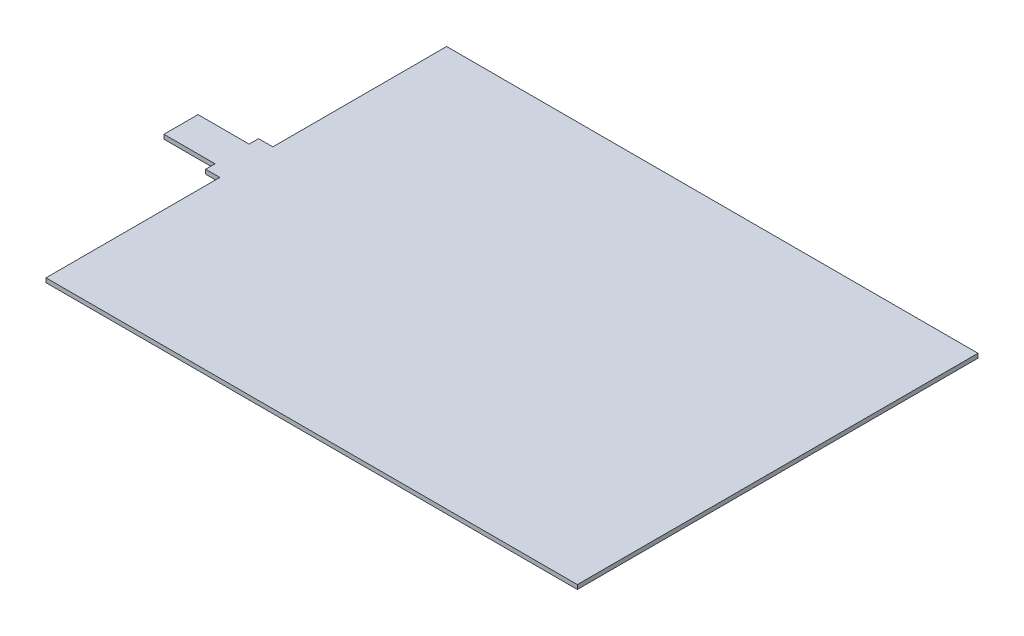
SolidWorks part; units mm, degrees
ref_plane "Front Plane" through (0, 0, 0) normal (0, 0, 1) x (1, 0, 0)
ref_plane "Top Plane" through (0, 0, 0) normal (0, 1, 0) x (1, 0, 0)
ref_plane "Right Plane" through (0, 0, 0) normal (1, 0, 0) x (0, 0, -1)
sketch "Sketch1" plane through (0, 0, 0) normal (0, 1, 0) x (1, 0, 0)
  line L0 (-93.5, 9.325) -> (-93.5, 70.5)
  line L1 (-93.5, -70.5) -> (93.5, -70.5)
  line L2 (-93.5, -70.5) -> (-93.5, -9.325)
  line L3 (-93.5, 70.5) -> (93.5, 70.5)
  line L4 (93.5, -70.5) -> (93.5, 70.5)
  line L5 (-93.5, -70.5) -> (93.5, 70.5) construction
  line L6 (-93.5, 70.5) -> (93.5, -70.5) construction
  line L7 (-98.5, -9.325) -> (-93.5, -9.325)
  line L8 (-98.5, -9.325) -> (-98.5, 9.325)
  line L9 (-98.5, 9.325) -> (-93.5, 9.325)
  point P0 (0, 0)
  point P6 (-98.5, 0)
  point P7 (0, 0)
  point P10 (0, 0)
  dimension "D1" = 187
  dimension "D2" = 141
  dimension "D3" = 18.65
  dimension "D4" = 5
extrude "Boss-Extrude1" add sketch "Sketch1" along normal blind 1.5
sketch "Sketch2" plane through (0, 1.5, 0) normal (0, 1, 0) x (1, 0, 0)
  line L0 (-98.5, 9.325) -> (-98.5, -9.325) construction
  line L1 (-98.5, 6) -> (-116.5, 6)
  line L2 (-98.5, 6) -> (-98.5, -6)
  line L3 (-98.5, -6) -> (-116.5, -6)
  line L4 (-116.5, 6) -> (-116.5, -6)
  point P6 (-98.5, 0)
  dimension "D1" = 12
  dimension "D2" = 18
extrude "Boss-Extrude2" add sketch "Sketch2" against normal up to surface (1.5 mm away) up to face at (-48, 0, 0)
